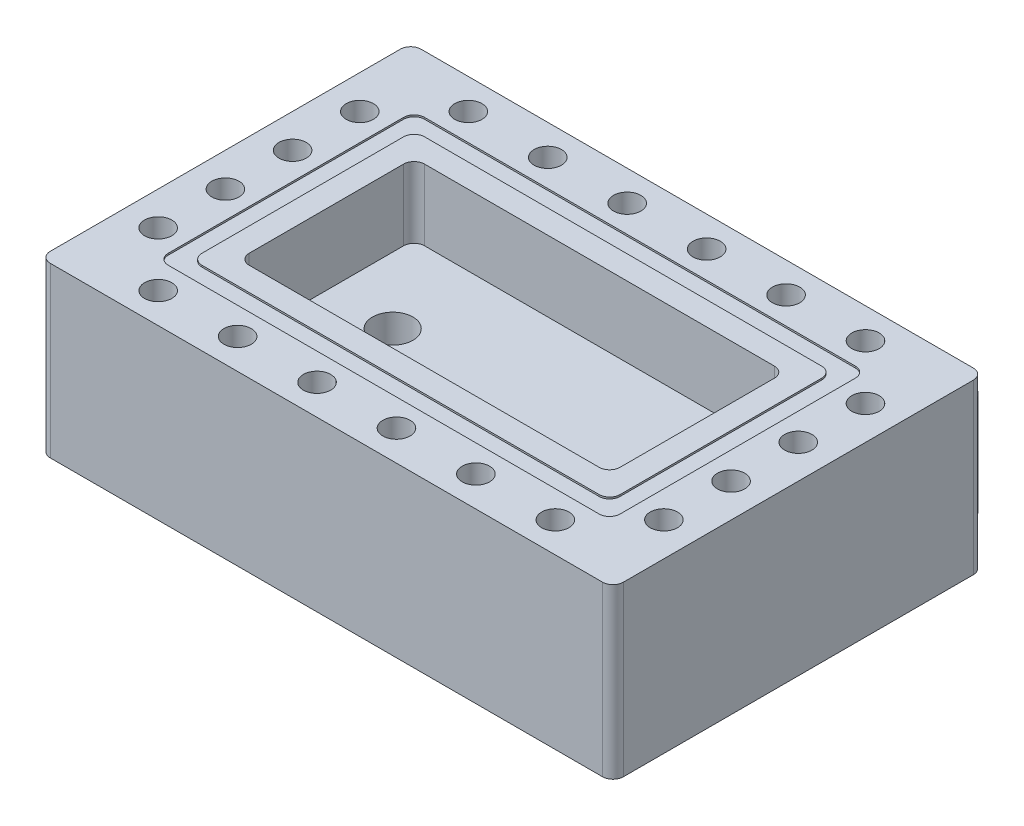
SolidWorks part; units mm, degrees
ref_plane "Front Plane" through (0, 0, 0) normal (0, 0, 1) x (1, 0, 0)
ref_plane "Top Plane" through (0, 0, 0) normal (0, 1, 0) x (1, 0, 0)
ref_plane "Right Plane" through (0, 0, 0) normal (1, 0, 0) x (0, 0, -1)
sketch "Sketch1" plane through (0, 0, 0) normal (0, 1, 0) x (1, 0, 0)
  line L0 (80, 55) -> (85, 55)
  line L1 (0, 0) -> (85, 0)
  line L2 (0, 0) -> (0, 55)
  line L3 (0, 55) -> (60, 55)
  line L4 (85, 0) -> (85, 55)
  line L5 (70, 55) -> (70, 65) construction
  arc A0 (60, 55) -> (80, 55) centre (70, 55) cw
  circle A1 centre (70, 60) radius 2
  dimension "D3" = 10
  dimension "D5" = 4
  dimension "D1" = 85
  dimension "D2" = 55
  dimension "D4" = 25
extrude "Boss-Extrude1" add sketch "Sketch1" along normal blind 25
sketch "Sketch2" plane through (0, 25, 0) normal (0, 1, 0) x (1, 0, 0)
  line L0 (42.5, 14.5) -> (42.5, 0) construction
  line L1 (15, 40.5) -> (70, 40.5)
  line L2 (15, 40.5) -> (15, 14.5)
  line L3 (15, 14.5) -> (70, 14.5)
  line L4 (70, 40.5) -> (70, 14.5)
  line L5 (0, 0) -> (85, 0) construction
  line L6 (70, 27.5) -> (85, 27.5) construction
  line L7 (85, 0) -> (85, 55) construction
  line L8 (15, 27.5) -> (0, 27.5) construction
  line L9 (0, 55) -> (0, 0) construction
  line L10 (42.5, 40.5) -> (42.5, 55) construction
  line L12 (42.5, 55) -> (85, 55) construction
  dimension "D1" = 26
  dimension "D2" = 55
extrude "Cut-Extrude1" cut sketch "Sketch2" against normal blind 10.5
fillet "Fillet1" radius 1.55 10 edges at (15, 19.75, -40.5) (15, 19.75, -14.5) (70, 19.75, -14.5) (70, 19.75, -40.5) (0, 12.5, -55) (85, 12.5, 0) (0, 12.5, 0) (60, 12.5, -55) (80, 12.5, -55) (85, 12.5, -55)
sketch "Sketch3" plane through (0, 25, 0) normal (0, 1, 0) x (1, 0, 0)
  line L0 (42.5, 14.5) -> (42.5, 11) construction
  line L1 (11.5, 44) -> (73.5, 44)
  line L2 (11.5, 44) -> (11.5, 11)
  line L3 (11.5, 11) -> (73.5, 11)
  line L4 (73.5, 44) -> (73.5, 11)
  line L5 (9, 46.5) -> (76, 46.5)
  line L6 (9, 46.5) -> (9, 8.5)
  line L7 (9, 8.5) -> (76, 8.5)
  line L8 (76, 46.5) -> (76, 8.5)
  line L9 (16.55, 14.5) -> (68.45, 14.5) construction
  line L10 (42.5, 11) -> (42.5, 8.5) construction
  line L11 (42.5, 40.5) -> (42.5, 44) construction
  line L12 (68.45, 40.5) -> (16.55, 40.5) construction
  line L13 (42.5, 44) -> (42.5, 46.5) construction
  line L14 (70, 27.5) -> (73.5, 27.5) construction
  line L15 (70, 16.05) -> (70, 38.95) construction
  line L16 (73.5, 27.5) -> (76, 27.5) construction
  line L17 (15, 27.5) -> (11.5, 27.5) construction
  line L18 (15, 38.95) -> (15, 16.05) construction
  line L19 (11.5, 27.5) -> (9, 27.5) construction
  dimension "D1" = 2.5
  dimension "D2" = 3.5
extrude "Cut-Extrude2" cut sketch "Sketch3" against normal blind 0.25
fillet "Fillet2" radius 1.55 8 edges at (76, 24.875, -46.5) (73.5, 24.875, -44) (73.5, 24.875, -11) (76, 24.875, -8.5) (11.5, 24.875, -11) (9, 24.875, -8.5) (11.5, 24.875, -44) (9, 24.875, -46.5)
sketch "Sketch5" plane through (0, 25, 0) normal (0, 1, 0) x (1, 0, 0)
  line L0 (13.05, 50.5) -> (5, 42.45) construction
  line L1 (5, 42.45) -> (5, 32.4833) construction
  line L2 (5, 32.4833) -> (5, 22.5167) construction
  line L3 (5, 22.5167) -> (5, 12.55) construction
  line L4 (5, 12.55) -> (13.05, 4.5) construction
  line L5 (13.05, 4.5) -> (24.83, 4.5) construction
  line L6 (58.5545, 55) -> (1.55, 55) construction
  line L7 (24.83, 4.5) -> (36.61, 4.5) construction
  line L8 (36.61, 4.5) -> (48.39, 4.5) construction
  line L9 (48.39, 4.5) -> (60.17, 4.5) construction
  line L10 (60.17, 4.5) -> (71.95, 4.5) construction
  line L11 (71.95, 4.5) -> (80, 12.55) construction
  line L12 (80, 12.55) -> (80, 22.5167) construction
  line L13 (80, 22.5167) -> (80, 32.4833) construction
  line L14 (80, 32.4833) -> (80, 42.45) construction
  line L15 (80, 42.45) -> (71.95, 50.5) construction
  line L16 (71.95, 50.5) -> (60.17, 50.5) construction
  line L17 (60.17, 50.5) -> (48.39, 50.5) construction
  line L18 (48.39, 50.5) -> (36.61, 50.5) construction
  line L19 (36.61, 50.5) -> (24.83, 50.5) construction
  line L20 (24.83, 50.5) -> (13.05, 50.5) construction
  line L21 (42.5, 8.5) -> (42.5, 4.5) construction
  line L24 (10.55, 8.5) -> (74.45, 8.5) construction
  line L25 (42.5, 50.5) -> (42.5, 46.5) construction
  line L26 (74.45, 46.5) -> (10.55, 46.5) construction
  line L27 (5, 27.5) -> (9, 27.5) construction
  line L28 (9, 44.95) -> (9, 10.05) construction
  line L29 (76, 27.5) -> (80, 27.5) construction
  line L30 (76, 10.05) -> (76, 44.95) construction
  line L31 (13.05, 11) -> (13.05, 4.5) construction
  line L32 (11.5, 12.55) -> (5, 12.55) construction
  circle A0 centre (5, 42.45) radius 2.025
  circle A1 centre (5, 12.55) radius 2.025
  circle A2 centre (13.05, 4.5) radius 2.025
  circle A3 centre (71.95, 4.5) radius 2.025
  circle A5 centre (24.83, 4.5) radius 2.025
  circle A6 centre (36.61, 4.5) radius 2.025
  circle A7 centre (48.39, 4.5) radius 2.025
  circle A8 centre (60.17, 4.5) radius 2.025
  circle A9 centre (5, 32.4833) radius 2.025
  circle A10 centre (5, 22.5167) radius 2.025
  circle A11 centre (80, 42.45) radius 2.025
  circle A12 centre (80, 12.55) radius 2.025
  circle A13 centre (80, 22.5167) radius 2.025
  circle A14 centre (80, 32.4833) radius 2.025
  circle A15 centre (13.05, 50.5) radius 2.025
  circle A16 centre (24.83, 50.5) radius 2.025
  circle A17 centre (36.61, 50.5) radius 2.025
  circle A18 centre (48.39, 50.5) radius 2.025
  circle A19 centre (60.17, 50.5) radius 2.025
  circle A20 centre (71.95, 50.5) radius 2.025
  dimension "D2" = 4.05
  dimension "D1" = 4
extrude "Cut-Extrude4" cut sketch "Sketch5" against normal through all
sketch "Sketch6" plane through (0, 14.5, 0) normal (0, 1, 0) x (1, 0, 0)
  line L0 (24.83, 50.5) -> (24.83, 4.5) construction
  circle A0 centre (24.83, 27.5) radius 3
  dimension "D1" = 6
extrude "Cut-Extrude5" cut sketch "Sketch6" against normal through all
sketch "Sketch7" plane through (0, 25, 0) normal (0, 1, 0) x (1, 0, 0)
  line L0 (58.5545, 55) -> (81.4455, 55)
  arc A0 (60.0905, 56.342) -> (79.9095, 56.342) centre (70, 55) cw
  arc A1 (79.9095, 56.342) -> (60.0905, 56.342) centre (70, 55) ccw construction
  arc A2 (79.9095, 56.342) -> (81.4455, 55) centre (81.4455, 56.55) ccw
  arc A3 (58.5545, 55) -> (60.0905, 56.342) centre (58.5545, 56.55) ccw
extrude "Cut-Extrude6" cut sketch "Sketch7" against normal blind 10
